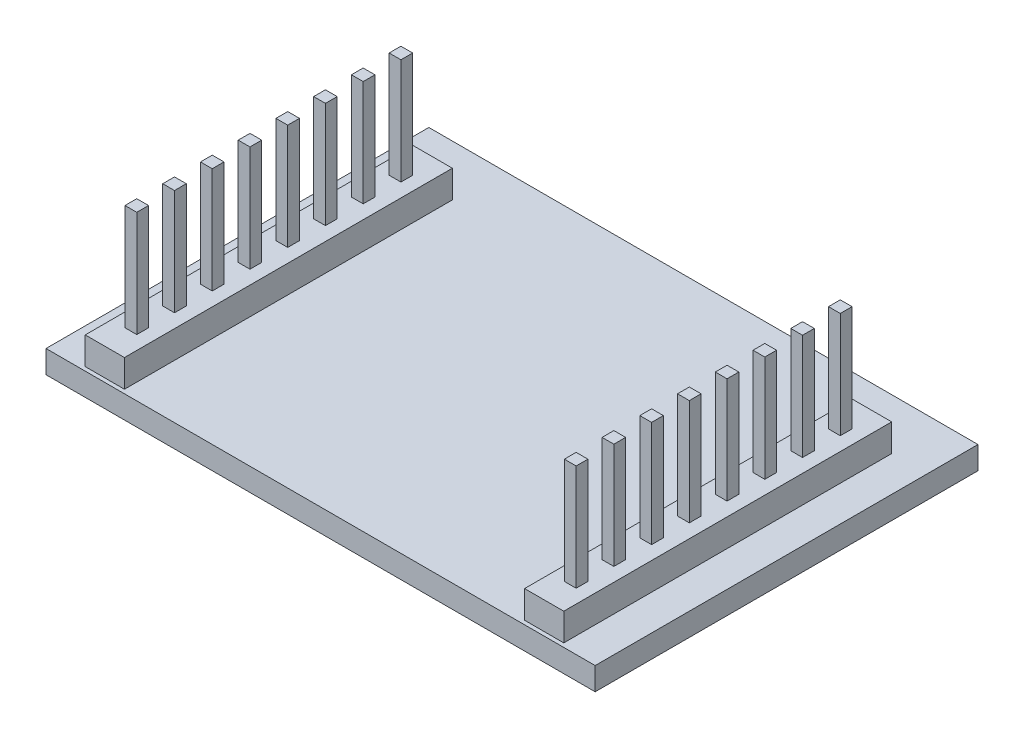
SolidWorks part; units mm, degrees
ref_plane "Front Plane" through (0, 0, 0) normal (0, 0, 1) x (1, 0, 0)
ref_plane "Top Plane" through (0, 0, 0) normal (0, 1, 0) x (1, 0, 0)
ref_plane "Right Plane" through (0, 0, 0) normal (1, 0, 0) x (0, 0, -1)
sketch "Sketch1" plane through (0, 0, 0) normal (0, 1, 0) x (1, 0, 0)
  line L1 (-17.5, -12.2) -> (17.5, -12.2)
  line L2 (-17.5, -12.2) -> (-17.5, 12.2)
  line L3 (-17.5, 12.2) -> (17.5, 12.2)
  line L4 (17.5, -12.2) -> (17.5, 12.2)
  point P0 (0, 0)
  dimension "D1" = 35
  dimension "D2" = 24.4
extrude "Boss-Extrude1" add sketch "Sketch1" along normal blind 1.45
sketch "Sketch2" plane through (0, 1.45, 0) normal (0, 1, 0) x (1, 0, 0)
  line L0 (-17.5, 12.2) -> (-17.5, -12.2) construction
  line L1 (-15.25, 8.95) -> (-12.75, 8.95)
  line L2 (-15.25, 8.95) -> (-15.25, -11.95)
  line L3 (-15.25, -11.95) -> (-12.75, -11.95)
  line L4 (-12.75, 8.95) -> (-12.75, -11.95)
  line L5 (-17.5, -12.2) -> (17.5, -12.2) construction
  line L6 (17.5, -12.2) -> (17.5, 12.2) construction
  line L7 (12.7518, 8.95) -> (15.25, 8.95)
  line L8 (12.7518, 8.95) -> (12.7518, -11.95)
  line L9 (12.7518, -11.95) -> (15.25, -11.95)
  line L10 (15.25, 8.95) -> (15.25, -11.95)
  dimension "D1" = 2.5
  dimension "D2" = 2.25
  dimension "D3" = 0.25
  dimension "D4" = 20.9
  dimension "D5" = 2.25
extrude "Boss-Extrude2" add sketch "Sketch2" along normal blind 1.75
sketch "Sketch3" plane through (0, 3.2, 0) normal (0, 1, 0) x (1, 0, 0)
  line L0 (-12.75, 8.95) -> (-15.25, 8.95) construction
  line L1 (-14.375, 7.295) -> (-13.625, 7.295)
  line L2 (-14.375, 7.295) -> (-14.375, 6.545)
  line L3 (-14.375, 6.545) -> (-13.625, 6.545)
  line L4 (-13.625, 7.295) -> (-13.625, 6.545)
  line L5 (-12.75, -11.95) -> (-12.75, 8.95) construction
  line L8 (-13.625, 4.89) -> (-14.375, 4.89)
  line L9 (-13.625, 4.89) -> (-13.625, 4.14)
  line L10 (-13.625, 4.14) -> (-14.375, 4.14)
  line L11 (-14.375, 4.89) -> (-14.375, 4.14)
  line L12 (-13.625, 2.485) -> (-14.375, 2.485)
  line L13 (-13.625, 2.485) -> (-13.625, 1.735)
  line L14 (-13.625, 1.735) -> (-14.375, 1.735)
  line L15 (-14.375, 2.485) -> (-14.375, 1.735)
  line L16 (-13.625, 0.08) -> (-14.375, 0.08)
  line L17 (-13.625, 0.08) -> (-13.625, -0.67)
  line L18 (-13.625, -0.67) -> (-14.375, -0.67)
  line L19 (-14.375, 0.08) -> (-14.375, -0.67)
  line L20 (-13.625, -2.325) -> (-14.375, -2.325)
  line L21 (-13.625, -2.325) -> (-13.625, -3.075)
  line L22 (-13.625, -3.075) -> (-14.375, -3.075)
  line L23 (-14.375, -2.325) -> (-14.375, -3.075)
  line L24 (-13.625, -4.73) -> (-14.375, -4.73)
  line L25 (-13.625, -4.73) -> (-13.625, -5.48)
  line L26 (-13.625, -5.48) -> (-14.375, -5.48)
  line L27 (-14.375, -4.73) -> (-14.375, -5.48)
  line L28 (-13.625, -7.135) -> (-14.375, -7.135)
  line L29 (-13.625, -7.135) -> (-13.625, -7.885)
  line L30 (-13.625, -7.885) -> (-14.375, -7.885)
  line L31 (-14.375, -7.135) -> (-14.375, -7.885)
  line L32 (-13.625, -9.54) -> (-14.375, -9.54)
  line L33 (-13.625, -9.54) -> (-13.625, -10.29)
  line L34 (-13.625, -10.29) -> (-14.375, -10.29)
  line L35 (-14.375, -9.54) -> (-14.375, -10.29)
  dimension "D1" = 0.75
  dimension "D2" = 0.75
  dimension "D3" = 1.655
  dimension "D4" = 0.875
  dimension "D5" = 1.655
  dimension "D6" = 1.655
  dimension "D7" = 1.655
  dimension "D8" = 1.655
  dimension "D9" = 1.655
  dimension "D10" = 1.655
  dimension "D11" = 1.655
extrude "Boss-Extrude3" add sketch "Sketch3" along normal blind 6.75
sketch "Sketch5" plane through (0, 3.2, 0) normal (0, 1, 0) x (1, 0, 0)
  line L0 (12.7518, 8.95) -> (12.7518, -11.95) construction
  line L1 (14.3768, 7.295) -> (13.6268, 7.295)
  line L2 (14.3768, 7.295) -> (14.3768, 6.545)
  line L3 (14.3768, 6.545) -> (13.6268, 6.545)
  line L4 (13.6268, 7.295) -> (13.6268, 6.545)
  line L6 (15.25, 8.95) -> (12.7518, 8.95) construction
  line L8 (14.3768, 4.89) -> (13.6268, 4.89)
  line L9 (14.3768, 4.89) -> (14.3768, 4.14)
  line L10 (14.3768, 4.14) -> (13.6268, 4.14)
  line L11 (13.6268, 4.89) -> (13.6268, 4.14)
  line L12 (14.3768, 2.485) -> (13.6268, 2.485)
  line L13 (14.3768, 2.485) -> (14.3768, 1.735)
  line L14 (14.3768, 1.735) -> (13.6268, 1.735)
  line L15 (13.6268, 2.485) -> (13.6268, 1.735)
  line L16 (14.3768, 0.08) -> (13.6268, 0.08)
  line L17 (14.3768, 0.08) -> (14.3768, -0.67)
  line L18 (14.3768, -0.67) -> (13.6268, -0.67)
  line L19 (13.6268, 0.08) -> (13.6268, -0.67)
  line L20 (14.3768, -2.325) -> (13.6268, -2.325)
  line L21 (14.3768, -2.325) -> (14.3768, -3.075)
  line L22 (14.3768, -3.075) -> (13.6268, -3.075)
  line L23 (13.6268, -2.325) -> (13.6268, -3.075)
  line L24 (14.3768, -4.73) -> (13.6268, -4.73)
  line L25 (14.3768, -4.73) -> (14.3768, -5.48)
  line L26 (14.3768, -5.48) -> (13.6268, -5.48)
  line L27 (13.6268, -4.73) -> (13.6268, -5.48)
  line L28 (14.3768, -7.135) -> (13.6268, -7.135)
  line L29 (14.3768, -7.135) -> (14.3768, -7.885)
  line L30 (14.3768, -7.885) -> (13.6268, -7.885)
  line L31 (13.6268, -7.135) -> (13.6268, -7.885)
  line L32 (14.3768, -9.54) -> (13.6268, -9.54)
  line L33 (14.3768, -9.54) -> (14.3768, -10.29)
  line L34 (14.3768, -10.29) -> (13.6268, -10.29)
  line L35 (13.6268, -9.54) -> (13.6268, -10.29)
  dimension "D1" = 0.75
  dimension "D2" = 0.75
  dimension "D3" = 0.875
  dimension "D4" = 1.655
  dimension "D5" = 1.655
  dimension "D6" = 1.655
  dimension "D7" = 1.655
  dimension "D8" = 1.655
  dimension "D9" = 1.655
  dimension "D10" = 1.655
  dimension "D11" = 1.655
extrude "Boss-Extrude4" add sketch "Sketch5" along normal blind 6.75
sketch "Sketch6" plane through (0, 0, 0) normal (0, -1, 0) x (-1, 0, 0)
  text T0 "Custom PCB"
extrude "Boss-Extrude5" add sketch "Sketch6" along normal blind 1
